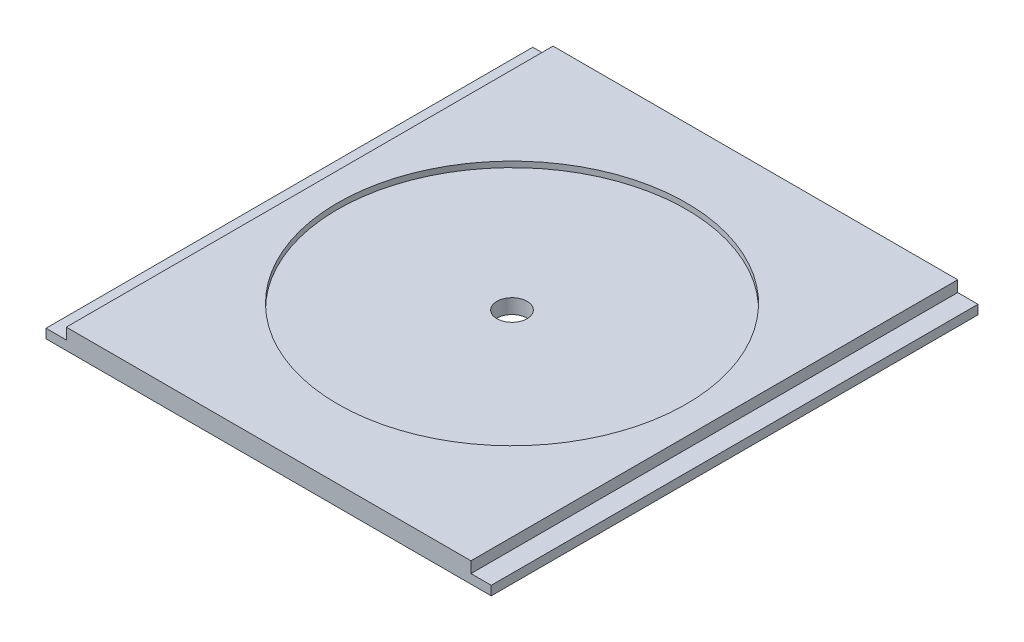
SolidWorks part; units mm, degrees
ref_plane "Front Plane" through (0, 0, 0) normal (0, 0, 1) x (1, 0, 0)
ref_plane "Top Plane" through (0, 0, 0) normal (0, 1, 0) x (1, 0, 0)
ref_plane "Right Plane" through (0, 0, 0) normal (1, 0, 0) x (0, 0, -1)
sketch "Sketch1" plane through (0, 0, 0) normal (0, 1, 0) x (1, 0, 0)
  line L1 (0, 0) -> (139.4003, 0)
  line L2 (0, 0) -> (0, 152.4)
  line L3 (0, 152.4) -> (139.4003, 152.4)
  line L4 (139.4003, 0) -> (139.4003, 152.4)
  dimension "D1" = 152.4
  dimension "D2" = 139.4003
extrude "Boss-Extrude1" add sketch "Sketch1" along normal blind 6.35
sketch "Sketch2" plane through (0, 6.35, 0) normal (0, 1, 0) x (1, 0, 0)
  line L0 (0, 0) -> (139.4003, 0) construction
  line L1 (0, 152.4) -> (6.35, 152.4)
  line L2 (0, 152.4) -> (0, 0)
  line L3 (0, 0) -> (6.35, 0)
  line L4 (6.35, 152.4) -> (6.35, 0)
  line L6 (139.4003, 152.4) -> (133.0503, 152.4)
  line L7 (139.4003, 152.4) -> (139.4003, 0)
  line L8 (139.4003, 0) -> (133.0503, 0)
  line L9 (133.0503, 152.4) -> (133.0503, 0)
  dimension "D1" = 6.35
  dimension "D2" = 6.35
extrude "Cut-Extrude1" cut sketch "Sketch2" against normal blind 3.4747
sketch "Sketch3" plane through (0, 6.35, 0) normal (0, 1, 0) x (1, 0, 0)
  line L0 (6.35, 0) -> (133.0503, 0) construction
  circle A0 centre (69.7001, 76.2) radius 54.5821
  point P5 (69.7001, 0)
  dimension "D1" = 109.1641
  dimension "D2" = 76.2
extrude "Cut-Extrude2" cut sketch "Sketch3" against normal blind 1.778
sketch "Sketch4" plane through (0, 4.572, 0) normal (0, 1, 0) x (1, 0, 0)
  circle A0 centre (69.7001, 76.2) radius 4.7219
  dimension "D1" = 9.4437
extrude "Cut-Extrude3" cut sketch "Sketch4" against normal through all
